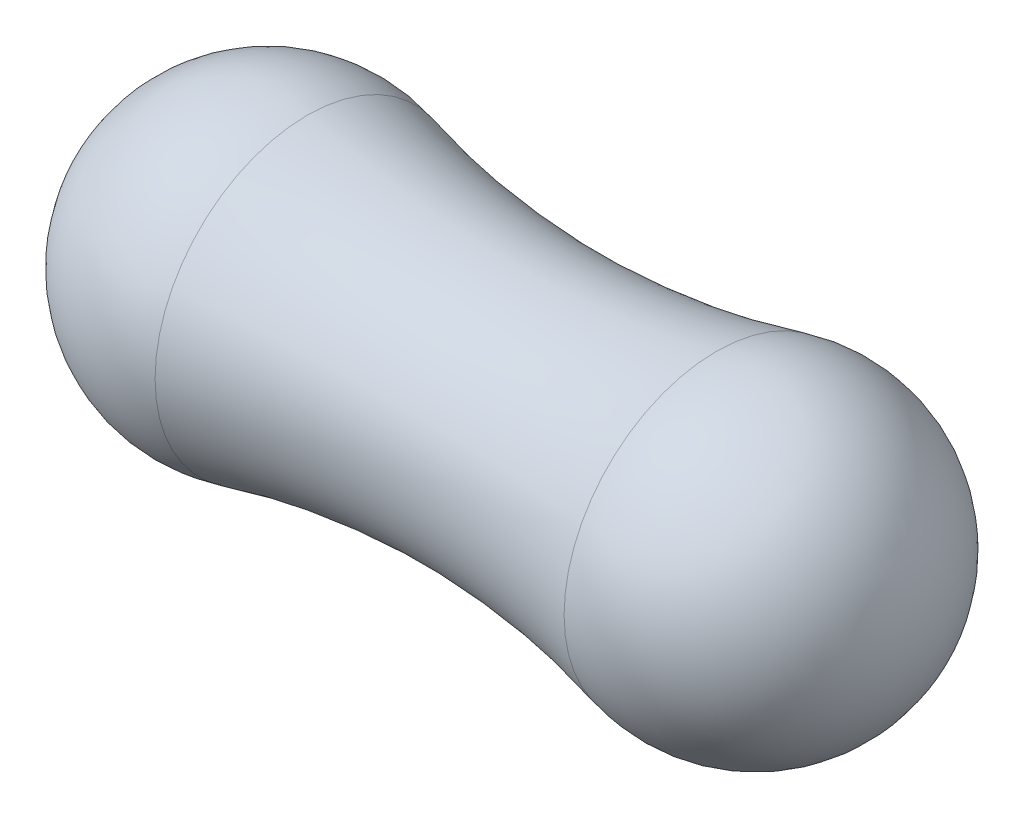
SolidWorks part; units mm, degrees
ref_plane "Front Plane" through (0, 0, 0) normal (0, 0, 1) x (1, 0, 0)
ref_plane "Top Plane" through (0, 0, 0) normal (0, 1, 0) x (1, 0, 0)
ref_plane "Right Plane" through (0, 0, 0) normal (1, 0, 0) x (0, 0, -1)
sketch "Sketch1" plane through (0, 0, 0) normal (0, 1, 0) x (1, 0, 0)
  line L0 (-2.54, 0) -> (2.54, 0)
  line L1 (2.54, 0) -> (5.3121, 0) construction
  arc A0 (-2.54, 0) -> (-1.295, 0.9637) centre (-1.5445, 0) cw
  arc A1 (-1.295, 0.9637) -> (1.295, 0.9637) centre (0, 5.9653) ccw
  arc A2 (1.295, 0.9637) -> (2.54, 0) centre (1.5445, 0) cw
  point P8 (0, 0)
  dimension "D1" = 5.08
revolve "Revolve1" add sketch "Sketch1" angle 360 about L1
